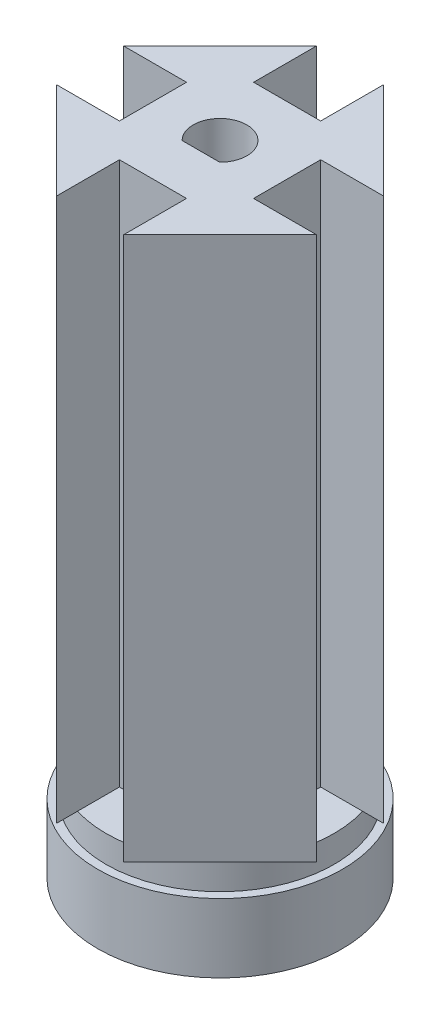
SolidWorks part; units mm, degrees
ref_plane "Front Plane" through (0, 0, 0) normal (0, 0, 1) x (1, 0, 0)
ref_plane "Top Plane" through (0, 0, 0) normal (0, 1, 0) x (1, 0, 0)
ref_plane "Right Plane" through (0, 0, 0) normal (1, 0, 0) x (0, 0, -1)
sketch "Sketch13" plane through (0, 0, 0) normal (0, 1, 0) x (1, 0, 0)
  circle A2 centre (0, 0) radius 18.25
  circle A3 centre (0, 0) radius 17
  dimension "D2" = 34
  dimension "D1" = 36.5
extrude "Boss-Extrude8" add sketch "Sketch13" along normal blind 0.255 and the other way blind 10
sketch "Sketch14" plane through (0, 0.255, 0) normal (0, 1, 0) x (1, 0, 0)
  line L0 (0, 0) -> (0, 3.425)
  line L1 (-2.0662, 3.425) -> (2.0662, 3.425)
  circle A0 centre (0, 0) radius 18.25
  circle A1 centre (0, 0) radius 4
  circle M2 centre (0, 0) radius 17
  dimension "D1" = 3.425
extrude "Boss-Extrude17" add sketch "Sketch14" along normal blind 5 contours A1 M2 | L1 A1
sketch "Sketch21" plane through (0, 5.255, 0) normal (0, 1, 0) x (1, 0, 0)
  circle A0 centre (0, 0) radius 20
  dimension "D1" = 40
extrude "Connector Cylinder" add sketch "Sketch21" along normal blind 80 and the other way blind 1
sketch "Sketch22" plane through (0, 85.255, 0) normal (0, 1, 0) x (1, 0, 0)
  line L0 (10, -5) -> (10, 5)
  line L4 (10, -5) -> (19.3649, -5)
  line L21 (-5, 19.3649) -> (-5, 10)
  line L39 (10, 5) -> (19.3649, 5)
  line L47 (-5, -10) -> (5, -10)
  line L51 (-10, -5) -> (-19.3649, -5)
  line L53 (-10, 5) -> (-19.3649, 5)
  line L54 (-10, 5) -> (-19.3649, 5)
  line L55 (-5, -10) -> (-5, -19.3649)
  line L58 (5, -10) -> (5, -19.3649)
  line L59 (-10, -5) -> (-10, 5)
  line L60 (-5, -10) -> (5, -10)
  line L64 (5, 19.3649) -> (5, 10)
  line L65 (-5, 10) -> (5, 10)
  line L67 (-10, 5) -> (-10, -5)
  circle A0 centre (0, 0) radius 20 construction
  circle M5 centre (0, 0) radius 20
  dimension "D1" = 10
  dimension "D2" = 10
  dimension "D3" = 9.3649
  dimension "D4" = 9.3649
  dimension "D5" = 10
  dimension "D6" = 9.3649
  dimension "D7" = 10
  dimension "D8" = 9.3649
sketch "Sketch23" plane through (0, 85.255, 0) normal (0, 1, 0) x (1, 0, 0)
  circle A0 centre (0, 0) radius 4
  dimension "D1" = 8
extrude "Cut-Extrude4" cut sketch "Sketch23" against normal blind 96.3
extrude "Connector Cylinder Cut" cut sketch "Sketch22" against normal blind 81 contours L58 L47 L55 M5 | L51 L59 L53 M5 | L21 L65 L64 M5 | L39 L0 L4 M5
sketch "Sketch24" plane through (0, 85.255, 0) normal (0, 1, 0) x (1, 0, 0)
  line L0 (-5, 19.3649) -> (-5, 10)
  line L1 (-19.3649, 5) -> (-10, 5)
  line L2 (-10, 5) -> (-5, 5)
  line L3 (5, 19.3649) -> (5, 5)
  line L4 (-5, 19.3649) -> (-5, 5)
  line L5 (-19.3649, -5) -> (-5, -5)
  line L6 (-5, 19.3649) -> (-19.3649, 5)
  line L7 (5, 19.3649) -> (19.3649, 5)
  line L8 (19.3649, -5) -> (5, -19.3649)
  line L9 (-5, -19.3649) -> (-19.3649, -5)
  line L10 (-5, -5) -> (-5, -19.3649)
  line L11 (5, -5) -> (5, -19.3649)
  line L12 (5, 5) -> (19.3649, 5)
  line L13 (5, -5) -> (19.3649, -5)
  circle A0 centre (0, 0) radius 20
  arc M4 (5, -19.3649) -> (19.3649, -5) centre (0, 0) ccw
  arc M8 (19.3649, 5) -> (5, 19.3649) centre (0, 0) ccw
  arc M12 (-5, 19.3649) -> (-19.3649, 5) centre (0, 0) ccw
  arc M16 (-19.3649, -5) -> (-5, -19.3649) centre (0, 0) ccw
extrude "Cut-Extrude5" cut sketch "Sketch24" against normal blind 81 contours L6 M12 | L7 M8 | L8 M4 | L9 M16
sketch "Sketch25" plane through (0, 0.255, 0) normal (0, -1, 0) x (1, 0, 0)
  line L0 (-2.8067, 2.85) -> (2.8067, 2.85)
  circle A0 centre (0, 0) radius 4
  circle M3 centre (0, 0) radius 4
  dimension "D1" = 8
  dimension "D2" = 2.85
extrude "Key Cut" add sketch "Sketch25" against normal blind 85 contours L0 M3
